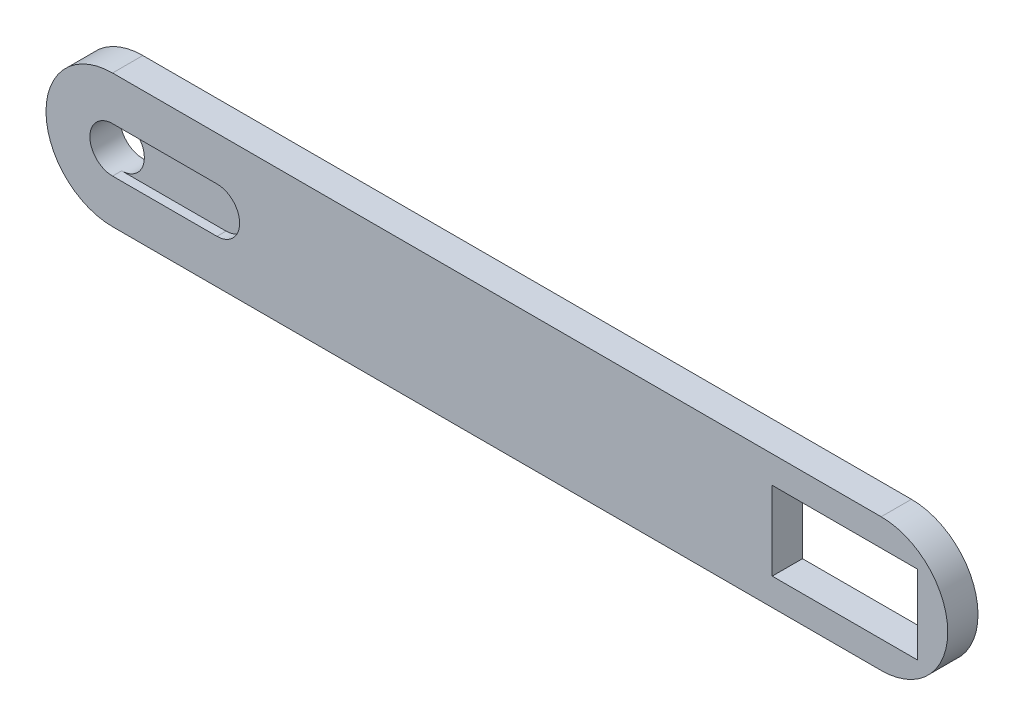
SolidWorks part; units mm, degrees
material "ABS"
ref_plane "Front Plane" through (0, 0, 0) normal (0, 0, 1) x (1, 0, 0)
ref_plane "Top Plane" through (0, 0, 0) normal (0, 1, 0) x (1, 0, 0)
ref_plane "Right Plane" through (0, 0, 0) normal (1, 0, 0) x (0, 0, -1)
sketch "Sketch1" plane through (0, 0, 0) normal (0, 0, 1) x (1, 0, 0)
  line L0 (0, 0) -> (127, 0)
  line L2 (127.1839, 22) -> (0, 22)
  line L3 (109, 17.5) -> (133, 17.5)
  line L4 (109, 17.5) -> (109, 4.5)
  line L5 (109, 4.5) -> (133, 4.5)
  line L6 (133, 17.5) -> (133, 4.5)
  arc A0 (127, 0) -> (127, 22) centre (127, 11) ccw
  arc A1 (0, 22) -> (0, 0) centre (0, 11) ccw
  circle A2 centre (0, 11) radius 3.75
  point P11 (0, 11)
  point P12 (127, 11)
  point P15 (127, 11)
  point P16 (133, 11)
  dimension "D3" = 7.5
  dimension "D1" = 127
  dimension "D2" = 22
  dimension "D4" = 24
  dimension "D5" = 13
  dimension "D6" = 6
extrude "Boss-Extrude1" add sketch "Sketch1" along normal blind 5 contours L2 A1 L0 A0 A2 L3 L6 L5 L4
sketch "Sketch3" plane through (0, 0, 5) normal (0, 0, 1) x (1, 0, 0)
  line L0 (0, 14.75) -> (17.25, 14.75)
  line L1 (0, 7.25) -> (17.25, 7.25)
  arc A0 (17.25, 14.75) -> (17.25, 7.25) centre (17.25, 11) cw
  circle A1 centre (0, 11) radius 3.75 construction
  arc A2 (0, 14.75) -> (0, 7.25) centre (0, 11) cw
  point P0 (0, 11)
  point P1 (17.25, 11)
  point P6 (0, 14.75)
  point P7 (0, 7.25)
  point P11 (21, 11)
  dimension "D1" = 21
extrude "Cut-Extrude1" cut sketch "Sketch3" against normal blind 1.5
